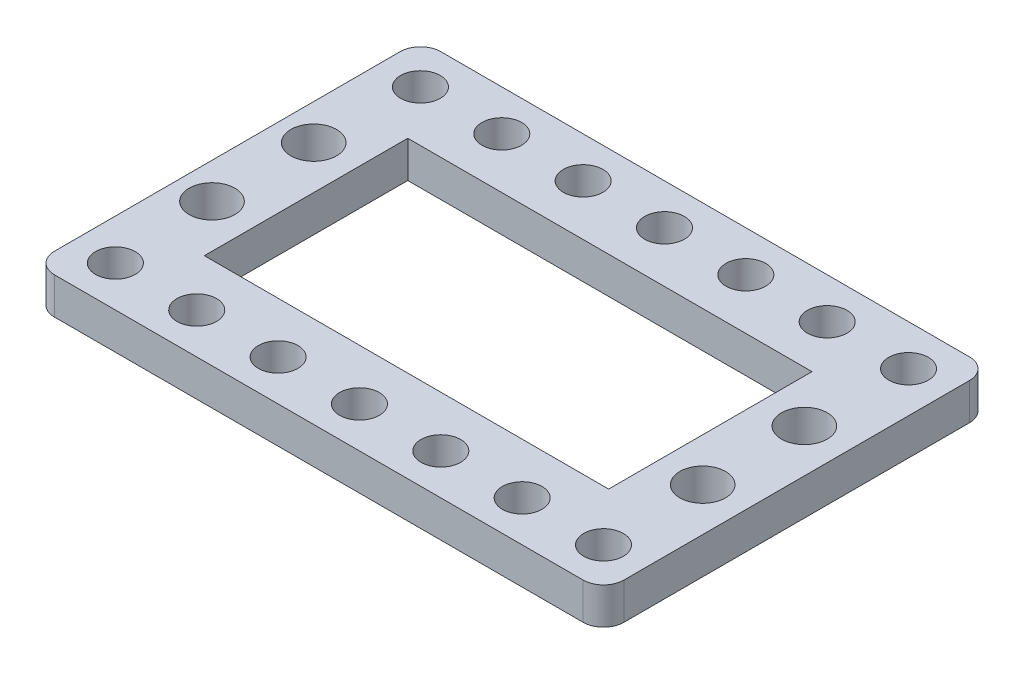
SolidWorks part; units mm, degrees
ref_plane "Front Plane" through (0, 0, 0) normal (0, 0, 1) x (1, 0, 0)
ref_plane "Top Plane" through (0, 0, 0) normal (0, 1, 0) x (1, 0, 0)
ref_plane "Right Plane" through (0, 0, 0) normal (1, 0, 0) x (0, 0, -1)
sketch "Sketch1" plane through (0, 0, 0) normal (0, 1, 0) x (1, 0, 0)
  line L1 (2, 0) -> (98, 0)
  line L2 (0, -2) -> (0, -36)
  line L3 (2, -38) -> (98, -38)
  line L4 (100, -2) -> (100, -36)
  arc A0 (98, -38) -> (100, -36) centre (98, -36) ccw
  arc A1 (0, -36) -> (2, -38) centre (2, -36) ccw
  arc A2 (2, 0) -> (0, -2) centre (2, -2) ccw
  arc A3 (98, 0) -> (100, -2) centre (98, -2) cw
  point P7 (100, -38)
  point P12 (0, 0)
  point P15 (100, 0)
  dimension "D3" = 2
  dimension "D1" = 100
  dimension "D2" = 38
extrude "Boss-Extrude1" add sketch "Sketch1" along normal blind 3.6
sketch "Sketch2" plane through (0, 3.6, 0) normal (0, 1, 0) x (1, 0, 0)
  line L0 (98, 0) -> (2, 0) construction
  line L1 (100, -36) -> (100, -2) construction
  line L2 (90, -4.0048) -> (0, -4.0048) construction
  line L3 (0, -2) -> (0, -36) construction
  line L4 (90, -34) -> (0, -34) construction
  line L5 (2, -38) -> (98, -38) construction
  line L7 (29.75, -9) -> (69.5, -9)
  line L8 (29.75, -9) -> (29.75, -29)
  line L9 (29.75, -29) -> (69.5, -29)
  line L10 (69.5, -9) -> (69.5, -29)
  circle A0 centre (90, -4.0048) radius 1.95
  circle A1 centre (82, -4.0048) radius 1.95
  circle A2 centre (18, -4.0048) radius 1.95
  circle A3 centre (26, -4.0048) radius 1.95
  circle A4 centre (34, -4.0048) radius 1.95
  circle A5 centre (42, -4.0048) radius 1.95
  circle A6 centre (50, -4.0048) radius 1.95
  circle A7 centre (58, -4.0048) radius 1.95
  circle A8 centre (66, -4.0048) radius 1.95
  circle A9 centre (74, -4.0048) radius 1.95
  circle A10 centre (90, -34) radius 1.95
  circle A11 centre (82, -34) radius 1.95
  circle A12 centre (18, -34) radius 1.95
  circle A13 centre (26, -34) radius 1.95
  circle A14 centre (34, -34) radius 1.95
  circle A15 centre (42, -34) radius 1.95
  circle A16 centre (50, -34) radius 1.95
  circle A17 centre (58, -34) radius 1.95
  circle A18 centre (66, -34) radius 1.95
  circle A19 centre (74, -34) radius 1.95
  dimension "D1" = 3.9
  dimension "D4" = 3.9
  dimension "D7" = 3.9
  dimension "D8" = 3.9
  dimension "D9" = 3.9
  dimension "D10" = 3.9
  dimension "D11" = 3.9
  dimension "D12" = 3.9
  dimension "D13" = 3.9
  dimension "D14" = 3.9
  dimension "D22" = 3.9
  dimension "D23" = 3.9
  dimension "D25" = 3.9
  dimension "D26" = 3.9
  dimension "D27" = 3.9
  dimension "D28" = 3.9
  dimension "D29" = 3.9
  dimension "D30" = 3.9
  dimension "D31" = 3.9
  dimension "D32" = 3.9
  dimension "D5" = 8
  dimension "D6" = 18
  dimension "D15" = 8
  dimension "D16" = 8
  dimension "D17" = 8
  dimension "D18" = 8
  dimension "D19" = 8
  dimension "D20" = 8
  dimension "D21" = 8
  dimension "D24" = 8
  dimension "D33" = 8
  dimension "D34" = 8
  dimension "D35" = 8
  dimension "D36" = 8
  dimension "D37" = 8
  dimension "D38" = 8
  dimension "D39" = 8
  dimension "D40" = 4.9952
  dimension "D41" = 10
  dimension "D42" = 18
  dimension "D43" = 30.5
  dimension "D44" = 9
  dimension "D45" = 29.75
  dimension "D46" = 9
  dimension "D47" = 10
  dimension "D48" = 5
extrude "Cut-Extrude1" cut sketch "Sketch2" against normal blind 3.6
sketch "Sketch4" plane through (0, 3.6, 0) normal (0, 1, 0) x (1, 0, 0)
  line L0 (98, 0) -> (2, 0) construction
  line L1 (78, 0) -> (100, 0)
  line L2 (78, 0) -> (78, -38)
  line L3 (78, -38) -> (100, -38)
  line L4 (100, 0) -> (100, -38)
  line L5 (2, -38) -> (98, -38) construction
  line L6 (100, -36) -> (100, -2) construction
  line L8 (0, 0) -> (22, 0)
  line L9 (0, 0) -> (0, -38)
  line L10 (0, -38) -> (22, -38)
  line L11 (22, 0) -> (22, -38)
  dimension "D1" = 22
  dimension "D2" = 22
extrude "Cut-Extrude2" cut sketch "Sketch4" against normal blind 10
fillet "Fillet1" radius 2 1 edges at (22, 1.8, 0)
fillet "Fillet2" radius 2 1 edges at (22, 1.8, 38)
fillet "Fillet3" radius 2 1 edges at (78, 1.8, 38)
fillet "Fillet4" radius 2 1 edges at (78, 1.8, 0)
sketch "Sketch5" plane through (0, 3.6, 0) normal (0, 1, 0) x (1, 0, 0)
  line L2 (78, -2) -> (78, -36) construction
  line L3 (76, 0) -> (24, 0) construction
  line L4 (22, -36) -> (22, -2) construction
  circle A0 centre (73.75, -14) radius 2.25
  circle A1 centre (73.75, -24) radius 2.25
  circle A2 centre (25.5, -14) radius 2.25
  circle A3 centre (25.5, -24) radius 2.25
  dimension "D1" = 4.5
  dimension "D4" = 4.5
  dimension "D7" = 4.5
  dimension "D8" = 4.5
  dimension "D2" = 4.25
  dimension "D3" = 4.25
  dimension "D5" = 10
  dimension "D6" = 14
  dimension "D9" = 10
  dimension "D10" = 3.5
  dimension "D11" = 14
  dimension "D12" = 3.5
extrude "Cut-Extrude3" cut sketch "Sketch5" against normal blind 10
